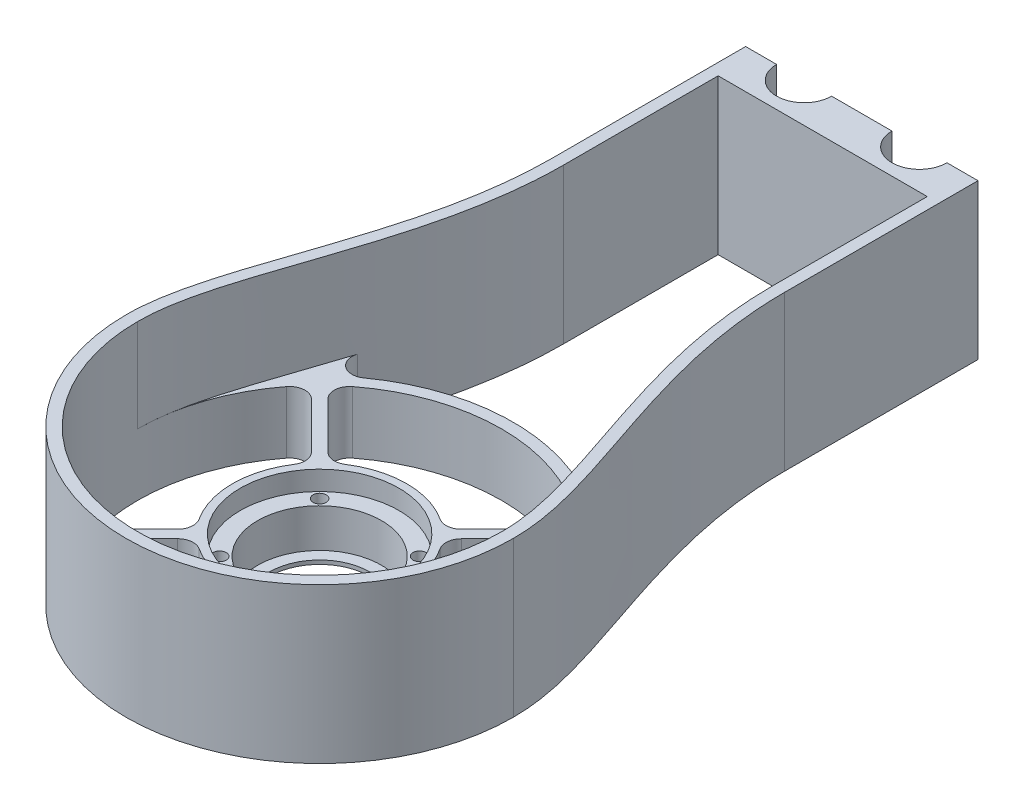
SolidWorks part; units mm, degrees
material "3.1355 (EN-AW 2024)"
ref_plane "Front" through (0, 0, 0) normal (0, 0, 1) x (1, 0, 0)
ref_plane "Top" through (0, 0, 0) normal (0, 1, 0) x (1, 0, 0)
ref_plane "Right" through (0, 0, 0) normal (1, 0, 0) x (0, 0, -1)
sketch "Эскиз1" plane through (0, 0, 0) normal (0, 1, 0) x (1, 0, 0)
  line L0 (0, 0) -> (8, 0)
  line L1 (0, 0) -> (0, -100) construction
  line L2 (0, -12.5175) -> (60, -12.5175) construction
  line L3 (8, 0) -> (22.2, 0) construction
  line L4 (30, -12.5175) -> (30, 0) construction
  line L5 (60, 0) -> (52, 0)
  line L6 (60, 0) -> (60, -100) construction
  line L7 (22.2, 0) -> (37.8, 0)
  line L8 (30, 0) -> (30, -140) construction
  line L9 (0, -80.7644) -> (0, -19.2352) construction
  line L10 (0, 0) -> (0, -50)
  line L11 (60, 0) -> (60, -50)
  arc A0 (22.2, 0) -> (8, 0) centre (15.1, 0) cw
  arc A1 (37.8, 0) -> (52, 0) centre (44.9, 0) ccw
  circle A2 centre (30, -140) radius 47 construction
  circle A3 centre (30, -140) radius 50 construction
  arc A4 (-20, -140) -> (80, -140) centre (30, -140) ccw
  spline S0 degree 3 poles (0, -50) (0, -86.1164) (-20.1607, -116.6426) (-20, -140) knots 0 0 0 0 1 1 1 1
  spline S1 degree 3 poles (60, -50) (60, -86.1164) (80.1607, -116.6426) (80, -140) knots 0 0 0 0 1 1 1 1
  dimension "D3" = 7.1
  dimension "D5" = 94
  dimension "D6" = 100
  dimension "D1" = 60
  dimension "D2" = 8
  dimension "D4" = 140
extrude "Бобышка-Вытянуть1" add sketch "Эскиз1" along normal blind 40
sketch "Эскиз2" plane through (0, 0, 0) normal (0, -1, 0) x (1, 0, 0)
  line L10 (3, 50) -> (3, 3)
  line L11 (3, 3) -> (5.4558, 3)
  line L12 (24.7442, 3) -> (35.2558, 3)
  line L13 (54.5442, 3) -> (57, 3)
  line L14 (57, 3) -> (57, 50)
  line L15 (0, 50) -> (0, 0)
  line L16 (60, 0) -> (60, 50)
  line L17 (52, 0) -> (60, 0)
  line L18 (22.2, 0) -> (37.8, 0)
  line L19 (0, 0) -> (8, 0)
  line L20 (0, 50) -> (0, 0) construction
  line L21 (60, 0) -> (60, 50) construction
  line L22 (52, 0) -> (60, 0) construction
  line L23 (22.2, 0) -> (37.8, 0) construction
  line L24 (0, 0) -> (8, 0) construction
  arc A6 (24.7442, 3) -> (5.4558, 3) centre (15.1, 0) ccw
  arc A7 (54.5442, 3) -> (35.2558, 3) centre (44.9, 0) ccw
  arc A8 (77, 139.9898) -> (-17, 139.9898) centre (30, 140) ccw
  arc A9 (80, 140) -> (-20, 140) centre (30, 140) ccw
  arc A10 (52, 0) -> (37.8, 0) centre (44.9, 0) ccw
  arc A11 (22.2, 0) -> (8, 0) centre (15.1, 0) ccw
  arc A12 (80, 140) -> (-20, 140) centre (30, 140) ccw construction
  arc A13 (52, 0) -> (37.8, 0) centre (44.9, 0) ccw construction
  arc A14 (22.2, 0) -> (8, 0) centre (15.1, 0) ccw construction
  spline S4 degree 1 poles (57, 50) (77, 139.9898) knots 0 0 1 1 construction
  spline S5 degree 1 poles (-17, 139.9898) (3, 50) knots 0 0 1 1 construction
  spline S6 degree 3 poles (2974.8733, 17.0098) (-3143.323, 462.9237) (3099.91, -31.1134) (-2928.364, -504.442) knots -3.750439 -3.750439 -3.750439 -3.750439 4.723475 4.723475 4.723475 4.723475 only from (-20, 140) to (0, 50)
  spline S7 degree 3 poles (2988.4431, -504.4482) (-3039.9457, -31.1192) (3203.3107, 462.9225) (-2914.8159, 17.014) knots -3.723512 -3.723512 -3.723512 -3.723512 4.750412 4.750412 4.750412 4.750412 only from (60, 50) to (80, 140)
  spline S8 degree 3 poles (-20, 140) (-20.1607, 116.6426) (0, 86.1164) (0, 50) knots 0 0 0 0 1 1 1 1 construction
  spline S9 degree 3 poles (60, 50) (60, 86.1164) (80.1607, 116.6426) (80, 140) knots 0 0 0 0 1 1 1 1 construction
  spline S10 degree 3 poles (57, 50) (57, 51.1576) (57.0406, 53.4814) (57.2737, 58.0563) (57.83, 63.6856) (58.8582, 70.2787) (60.6258, 78.8545) (63.4224, 89.1625) (67.2233, 100.8564) (70.9826, 111.8507) (73.6803, 120.399) (75.3443, 126.8384) (76.2901, 131.4596) (76.7833, 135.1228) (76.9778, 137.9476) (77.0047, 139.3043) (77, 139.9898) knots 0 0 0 0 0.031255 0.062509 0.125019 0.187528 0.250037 0.375056 0.500075 0.625093 0.750112 0.812622 0.875131 0.93764 0.968895 1.00015 1.00015 1.00015 1.00015
  spline S11 degree 3 poles (-17, 139.9898) (-17.0047, 139.3043) (-16.9778, 137.9476) (-16.7833, 135.1228) (-16.2901, 131.4596) (-15.3443, 126.8384) (-13.6803, 120.399) (-10.9826, 111.8507) (-7.2233, 100.8564) (-3.4224, 89.1625) (-0.6258, 78.8545) (1.1418, 70.2787) (2.17, 63.6856) (2.7263, 58.0563) (2.9594, 53.4814) (3, 51.1576) (3, 50) knots -0.00015 -0.00015 -0.00015 -0.00015 0.031105 0.06236 0.124869 0.187378 0.249888 0.374907 0.499925 0.624944 0.749963 0.812472 0.874981 0.937491 0.968745 1 1 1 1
  dimension "D1" = 0
  dimension "D2" = 3
extrude "Вырез-Вытянуть1" cut sketch "Эскиз2" against normal through all
sketch "Эскиз3" plane through (0, 0, 0) normal (0, -1, 0) x (1, 0, 0)
  circle A0 centre (30, 140) radius 13
  circle A1 centre (30, 140) radius 22.5
  dimension "D1" = 26
  dimension "D2" = 45
extrude "Бобышка-Вытянуть2" add sketch "Эскиз3" against normal blind 16 separate body
sketch "Эскиз4" plane through (0, 16, 0) normal (0, 1, 0) x (1, 0, 0)
  circle A2 centre (30, -140) radius 20.5
  dimension "D1" = 41
extrude "Вырез-Вытянуть2" cut sketch "Эскиз4" against normal blind 5
sketch "Эскиз5" plane through (0, 11, 0) normal (0, 1, 0) x (1, 0, 0)
  circle A0 centre (30, -140) radius 16
  dimension "D1" = 32
extrude "Вырез-Вытянуть3" cut sketch "Эскиз5" against normal blind 10
sketch "Эскиз6" plane through (0, 11, 0) normal (0, 1, 0) x (1, 0, 0)
  line L0 (30, -140) -> (11.75, -140) construction
  line L1 (30, -140) -> (17.0953, -127.0953) construction
  line L2 (30, -140) -> (42.9047, -127.0953) construction
  line L3 (30, -140) -> (42.9047, -152.9047) construction
  line L4 (30, -140) -> (17.0953, -152.9047) construction
  circle A0 centre (30, -140) radius 18.25 construction
  point P11 (30, -140)
  dimension "D1" = 36.5
  dimension "D2" = 45
  dimension "D3" = 4
hole_wizard "Отверстие с зазором M31" positions "Эскиз8" profile "Эскиз7" hole size "M3" standard "Ansi Metric" end condition through all
sketch "Эскиз8" plane through (0, 11, 0) normal (0, 1, 0) x (1, 0, 0)
  point P0 (17.0953, -127.0953)
  point P3 (42.9047, -127.0953)
  point P6 (42.9047, -152.9047)
  point P9 (17.0953, -152.9047)
sketch "Эскиз7" plane through (17.0953, 11, 127.0953) normal (1, 0, 0) x (0, 0, 1)
  line L0 (0, 0) -> (0, 11)
  line L1 (0, 11) -> (1.7, 11)
  line L2 (1.7, 11) -> (1.7, 0)
  line L5 (1.7, 0) -> (0, 0)
  line L11 (0, -6.35) -> (0, 107.95) construction
  dimension "Диаметр сквозного отверстия" = 3.4
  dimension "Глубина сквозного отверстия" = 11
sketch "Эскиз9" plane through (0, 0, 0) normal (0, -1, 0) x (1, 0, 0)
  arc A0 (-10.5903, 110.8036) -> (70.5903, 110.8036) centre (30, 140) ccw
  arc A2 (-17, 139.9898) -> (77, 139.9898) centre (30, 140) ccw
  spline S1 degree 3 poles (143.2369, 2133.3498) (16.7126, 172.1608) (-19.1444, 169.4132) (-16.7833, 135.1228) (-16.2901, 131.4596) (-15.3443, 126.8384) (-13.6803, 120.399) (-10.9826, 111.8507) (-7.2233, 100.8564) (-3.4224, 89.1625) (-0.6258, 78.8545) (1.1418, 70.2787) (2.17, 63.6856) (2.7263, 58.0563) (6.108, -8.3151) (-50.2325, -100.9504) (-382.6796, 2011.3771) knots -1.392758 -1.392758 -1.392758 -1.392758 0.031105 0.06236 0.124869 0.187378 0.249888 0.374907 0.499925 0.624944 0.749963 0.812472 0.874981 0.937491 0.968745 2.688738 2.688738 2.688738 2.688738 only from (-17, 139.9898) to (3, 50) construction
  spline S2 degree 3 poles (442.6796, 2011.3774) (110.2325, -100.9504) (53.892, -8.3151) (57.2737, 58.0563) (57.83, 63.6856) (58.8582, 70.2787) (60.6258, 78.8545) (63.4224, 89.1625) (67.2233, 100.8564) (70.9826, 111.8507) (73.6803, 120.399) (75.3443, 126.8384) (76.2901, 131.4596) (76.7833, 135.1228) (79.1444, 169.4133) (43.287, 172.1608) (-83.2388, 2133.3791) knots -1.688738 -1.688738 -1.688738 -1.688738 0.031255 0.062509 0.125019 0.187528 0.250037 0.375056 0.500075 0.625093 0.750112 0.812622 0.875131 0.93764 0.968895 2.392765 2.392765 2.392765 2.392765 only from (57, 50) to (77, 139.9898) construction
  spline S3 degree 3 poles (70.5903, 110.8036) (70.6927, 111.1127) (71.9681, 114.9735) (73.6803, 120.399) (75.3443, 126.8384) (76.2901, 131.4596) (76.7833, 135.1228) (76.9778, 137.9476) (77.0047, 139.3043) (77, 139.9898) knots 0.614251 0.614251 0.614251 0.614251 0.625093 0.750112 0.812622 0.875131 0.93764 0.968895 1.00015 1.00015 1.00015 1.00015
  spline S4 degree 3 poles (-17, 139.9898) (-17.0047, 139.3043) (-16.9778, 137.9476) (-16.7833, 135.1228) (-16.2901, 131.4596) (-15.3443, 126.8384) (-13.6803, 120.399) (-11.9681, 114.9735) (-10.6927, 111.1127) (-10.5903, 110.8036) knots -0.00015 -0.00015 -0.00015 -0.00015 0.031105 0.06236 0.124869 0.187378 0.249888 0.374907 0.385749 0.385749 0.385749 0.385749
extrude "Бобышка-Вытянуть3" add sketch "Эскиз9" against normal up to surface (16 mm away) up to face at (30, 16, 160.5)
sketch "Эскиз10" plane through (0, 0, 0) normal (0, -1, 0) x (1, 0, 0)
  line L0 (30, 140) -> (-3.2268, 106.7588) construction
  line L1 (30, 140) -> (-17, 139.9898) construction
  line L2 (13.0616, 154.8102) -> (-4.2847, 172.149)
  line L3 (15.1898, 123.0616) -> (-2.149, 105.7153)
  line L4 (13.068, 125.1825) -> (-4.2708, 107.8362)
  line L5 (31.0609, 138.9396) -> (-2.1659, 105.6984) construction
  line L6 (15.1825, 156.932) -> (-2.1638, 174.2708)
  line L7 (44.8102, 156.9384) -> (62.149, 174.2847)
  line L8 (46.932, 154.8175) -> (64.2708, 172.1638)
  line L9 (46.9384, 125.1898) -> (64.2847, 107.851)
  line L10 (44.8175, 123.068) -> (62.1638, 105.7292)
  circle A0 centre (30, 140) radius 22.5 construction
  arc A1 (13.068, 125.1825) -> (15.1898, 123.0616) centre (30, 140) ccw
  circle A2 centre (30, 140) radius 47 construction
  arc A3 (-4.2708, 107.8362) -> (-2.149, 105.7153) centre (30, 140) ccw
  arc A4 (-2.1638, 174.2708) -> (-4.2847, 172.149) centre (30, 140) ccw
  arc A5 (15.1825, 156.932) -> (13.0616, 154.8102) centre (30, 140) ccw
  arc A6 (64.2708, 172.1638) -> (62.149, 174.2847) centre (30, 140) ccw
  arc A7 (46.932, 154.8175) -> (44.8102, 156.9384) centre (30, 140) ccw
  arc A8 (62.1638, 105.7292) -> (64.2847, 107.851) centre (30, 140) ccw
  arc A9 (44.8175, 123.068) -> (46.9384, 125.1898) centre (30, 140) ccw
  point P5 (28.9391, 141.0604)
  point P9 (-4.2877, 107.8192)
  point P29 (30, 140)
  point P36 (30, 140)
  dimension "D1" = 45
  dimension "D2" = 4
  dimension "D3" = 1.5
extrude "Бобышка-Вытянуть4" add sketch "Эскиз10" against normal up to surface (16 mm away) up to face at (30, 16, 160.5)
fillet "Скругление1" radius 4 2 edges
fillet "Скругление2" radius 4 18 edges at (-4.2847, 8, 172.149) (-2.1638, 8, 174.2708) (15.1825, 8, 156.932) (13.0616, 8, 154.8102) (62.149, 8, 174.2847) (64.2708, 8, 172.1638) (46.932, 8, 154.8175) (44.8102, 8, 156.9384) (64.2847, 8, 107.851) (62.1638, 8, 105.7292) (44.8175, 8, 123.068) (46.9384, 8, 125.1898) (-2.149, 8, 105.7153) (-4.2708, 8, 107.8362) (13.068, 8, 125.1825) (15.1898, 8, 123.0616)
sketch "Эскиз11" plane through (0, 40, 0) normal (0, 1, 0) x (1, 0, 0)
  line L0 (3, -50) -> (3, -3) construction
  line L1 (3, -10.1) -> (57, -10.1)
  line L2 (57, -3) -> (57, -50) construction
  line L3 (54.5442, -3) -> (57, -3) construction
  line L4 (24.7442, -3) -> (35.2558, -3) construction
  line L5 (3, -3) -> (5.4558, -3) construction
  line L6 (54.5442, -3) -> (57, -3)
  line L7 (24.7442, -3) -> (35.2558, -3)
  line L8 (3, -3) -> (5.4558, -3)
  line L9 (3, -10.1) -> (3, -3)
  line L10 (57, -3) -> (57, -10.1)
  arc A0 (5.4558, -3) -> (24.7442, -3) centre (15.1, 0) ccw construction
  arc A1 (5.4558, -3) -> (24.7442, -3) centre (15.1, 0) ccw
  arc A2 (35.2558, -3) -> (54.5442, -3) centre (44.9, 0) ccw construction
  arc A3 (35.2558, -3) -> (54.5442, -3) centre (44.9, 0) ccw
  line M2 (3, -50) -> (3, -3)
  line M3 (3, -3) -> (5.4558, -3)
  arc M4 (5.4558, -3) -> (24.7442, -3) centre (15.1, 0) ccw
  line M5 (24.7442, -3) -> (35.2558, -3)
  arc M6 (35.2558, -3) -> (54.5442, -3) centre (44.9, 0) ccw
  line M7 (54.5442, -3) -> (57, -3)
  line M8 (57, -3) -> (57, -50)
extrude "Бобышка-Вытянуть5" add sketch "Эскиз11" against normal through all contours L1 M4 M6 M5 | L1 M6 M8 M7 | L1 M2 M4 M3
